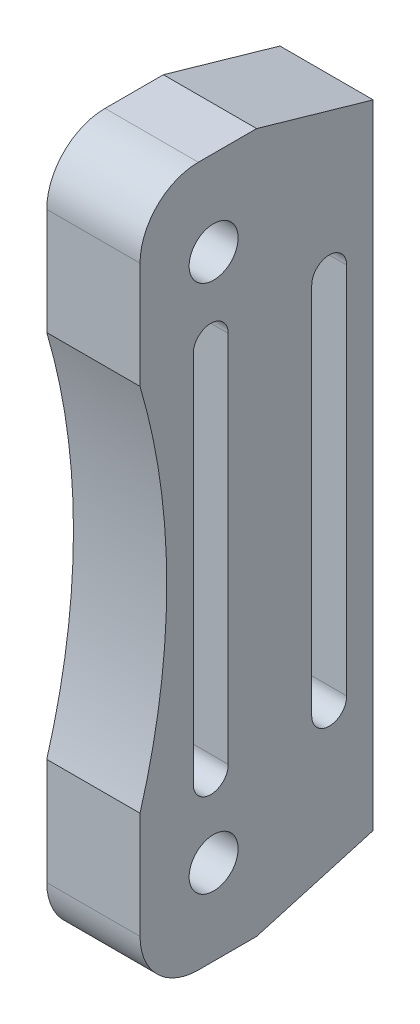
SolidWorks part; units mm, degrees
ref_plane "Front Plane" through (0, 0, 0) normal (0, 0, 1) x (1, 0, 0)
ref_plane "Top Plane" through (0, 0, 0) normal (0, 1, 0) x (1, 0, 0)
ref_plane "Right Plane" through (0, 0, 0) normal (1, 0, 0) x (0, 0, -1)
sketch "Sketch1" plane through (0, 0, 0) normal (1, 0, 0) x (0, 0, -1)
  line L0 (-10, 0) -> (10, 0) construction
  line L1 (-10, 30) -> (10, 30)
  line L2 (-10, 30) -> (-10, -30)
  line L3 (-10, -30) -> (10, -30)
  line L4 (10, 30) -> (10, -30)
  line L5 (-10, 30) -> (10, -30) construction
  line L6 (-10, -30) -> (10, 30) construction
  line L7 (0, 30) -> (0, -30) construction
  line L8 (-10, 0) -> (-63.71, 0) construction
  circle A1 centre (-3.69, 22.685) radius 2.1
  circle A2 centre (-3.69, -22.685) radius 2.1
  circle A4 centre (-63.71, 0) radius 56
  point P0 (0, 0)
  dimension "D3" = 45.37
  dimension "D8" = 112
  dimension "D1" = 60
  dimension "D2" = 20
  dimension "D4" = 6.31
  dimension "D7" = 53.71
extrude "Boss-Extrude1" add sketch "Sketch1" against normal blind 8
fillet "Fillet1" radius 5 2 edges at (-4, -30, 10) (-4, 30, 10)
chamfer "Chamfer1" distance 10 angle 16 2 edges at (-4, -30, -10) (-4, 30, -10)
sketch "Sketch2" plane through (0, 0, 0) normal (1, 0, 0) x (0, 0, -1)
  line L0 (-7.71, 0) -> (10, 0) construction
  line L1 (10, 27.1325) -> (10, -27.1325) construction
  line L2 (1.145, 0) -> (1.145, 29.6717) construction
  line L3 (10, 27.1325) -> (0, 30) construction
  line L4 (6.225, 16) -> (6.225, -16) construction
  line L5 (7.725, 16) -> (7.725, -16)
  line L6 (4.725, 16) -> (4.725, -16)
  line L7 (-3.935, 16) -> (-3.935, -16) construction
  line L8 (-5.435, 16) -> (-5.435, -16)
  line L9 (-2.435, 16) -> (-2.435, -16)
  arc A0 (-10, -15.8504) -> (-10, 15.8504) centre (-63.71, 0) ccw construction
  arc A1 (7.725, 16) -> (4.725, 16) centre (6.225, 16) ccw
  arc A2 (4.725, -16) -> (7.725, -16) centre (6.225, -16) ccw
  arc A3 (-5.435, 16) -> (-2.435, 16) centre (-3.935, 16) cw
  arc A4 (-2.435, -16) -> (-5.435, -16) centre (-3.935, -16) cw
  point P13 (6.225, 0)
  point P18 (6.225, 17.5)
  point P19 (6.225, -17.5)
  point P23 (-3.935, 0)
  dimension "D1" = 1.5
  dimension "D2" = 35
  dimension "D3" = 5.08
extrude "Cut-Extrude1" cut sketch "Sketch2" against normal up to next
